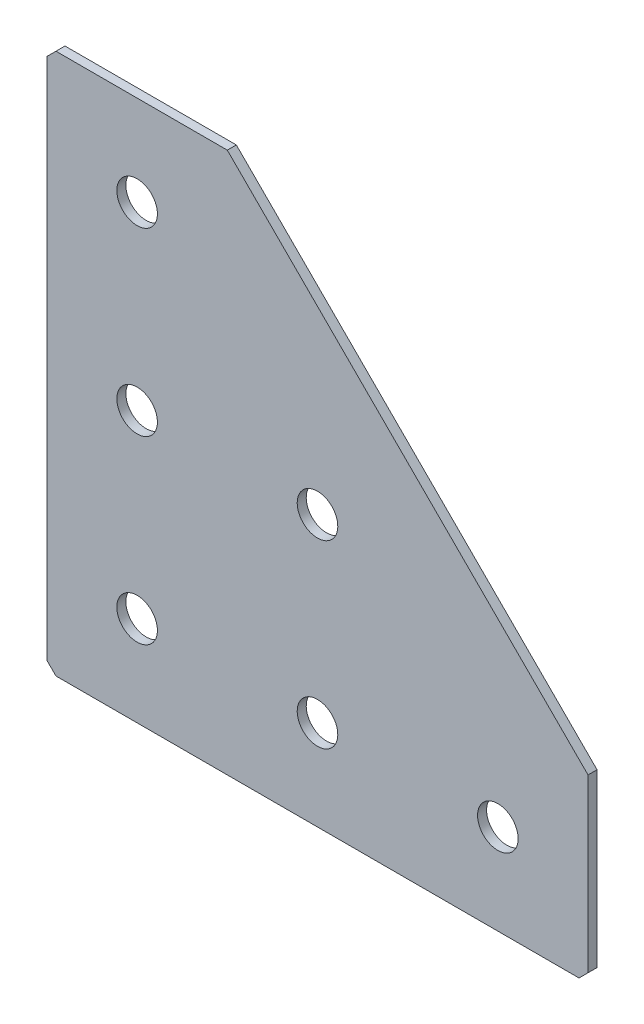
SolidWorks part; units mm, degrees
material "Простая углеродистая сталь"
ref_plane "Спереди(Плоскость XY)" through (0, 0, 0) normal (0, 0, 1) x (1, 0, 0)
ref_plane "Сверху(Плоскость XZ)" through (0, 0, 0) normal (0, 1, 0) x (1, 0, 0)
ref_plane "Справа(Плоскость ZY)" through (0, 0, 0) normal (1, 0, 0) x (0, 0, -1)
sketch "Эскиз1" plane through (0, 0, 0) normal (0, 0, -1) x (1, 0, 0)
  line L0 (0, 0) -> (0, 120)
  line L1 (0, 120) -> (120, 120)
  line L2 (120, 120) -> (120, 80)
  line L3 (120, 80) -> (40, 80) construction
  line L4 (40, 80) -> (40, 0) construction
  line L5 (40, 0) -> (0, 0)
  line L6 (40, 0) -> (120, 80)
  dimension "D1" = 120
  dimension "D3" = 40
extrude "Бобышка-Вытянуть1" add sketch "Эскиз1" along normal blind 2
hole_wizard "Отверстие с зазором M81" positions "Эскиз2" profile "Эскиз3" hole size "M8" standard "DIN" end condition through all
sketch "Эскиз2" plane through (0, 0, -2) normal (0, 0, -1) x (1, 0, 0)
  line L6 (20, 100) -> (60, 100) construction
  line L7 (60, 100) -> (100, 100) construction
  line L9 (20, 100) -> (20, 60) construction
  line L10 (20, 60) -> (20, 20) construction
  line L12 (60, 100) -> (60, 60) construction
  line L14 (0, 120) -> (0, 0) construction
  line L15 (120, 120) -> (0, 120) construction
  point P0 (60, 100)
  point P2 (20, 100)
  point P4 (20, 60)
  point P6 (20, 20)
  point P21 (100, 100)
  point P22 (60, 60)
  dimension "D1" = 40
  dimension "D2" = 20
  dimension "D3" = 20
sketch "Эскиз3" plane through (60, -100, -2) normal (1, 0, 0) x (0, 1, 0)
  line L0 (0, 0) -> (0, 2)
  line L1 (0, 2) -> (4.5, 2)
  line L2 (4.5, 2) -> (4.5, 0)
  line L5 (4.5, 0) -> (0, 0)
  line L11 (0, -6.35) -> (0, 107.95) construction
  dimension "Диаметр сквозного отверстия" = 9
  dimension "Глубина сквозного отверстия" = 2
chamfer "Фаска1" distance 2 angle 45 3 edges at (0, 0, -1) (120, -120, -1) (0, -120, -1)
